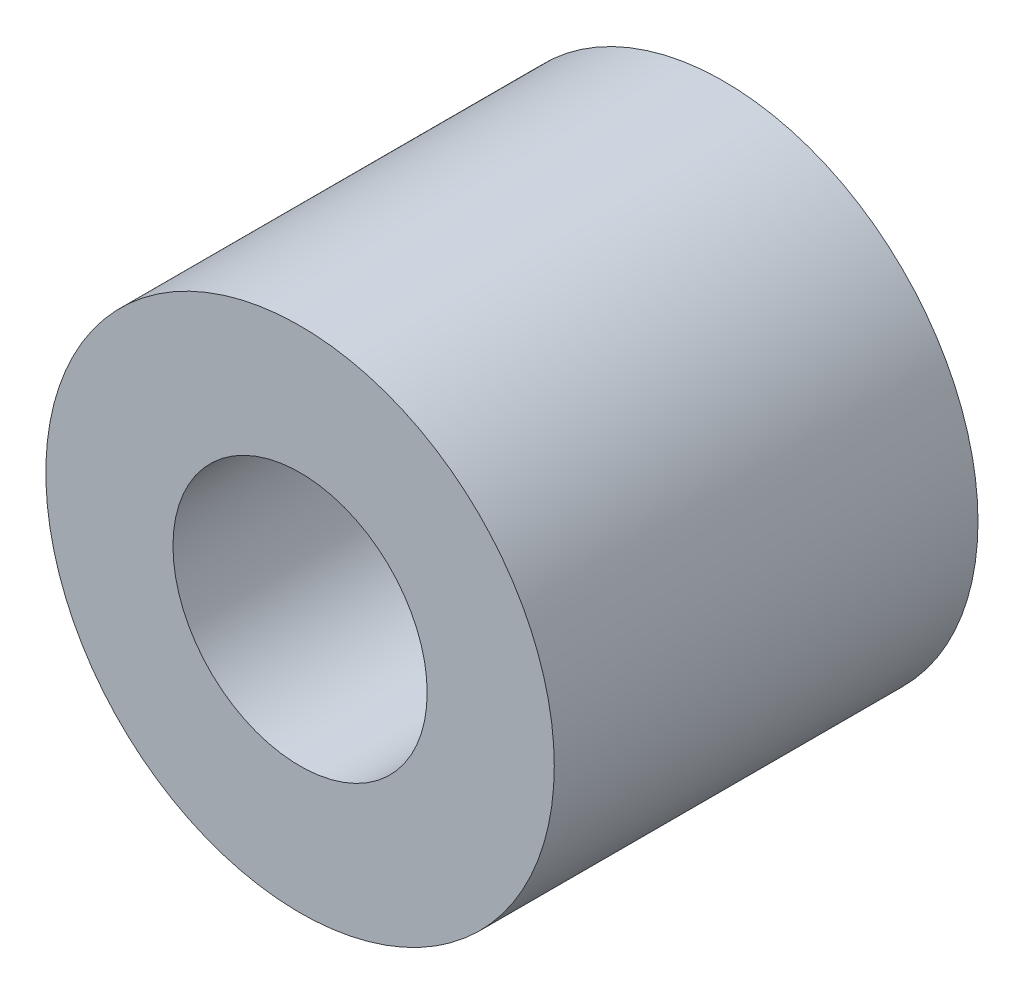
SolidWorks part; units mm, degrees
ref_plane "Alzado" through (0, 0, 0) normal (0, 0, 1) x (1, 0, 0)
ref_plane "Planta" through (0, 0, 0) normal (0, 1, 0) x (1, 0, 0)
ref_plane "Vista lateral" through (0, 0, 0) normal (1, 0, 0) x (0, 0, -1)
sketch "Croquis1" plane through (0, 0, 0) normal (0, 0, 1) x (1, 0, 0)
  circle A0 centre (0, 0) radius 1.5
  circle A1 centre (0, 0) radius 3
extrude "Saliente-Extruir1" add sketch "Croquis1" along normal blind 5 contours A0 | A1
